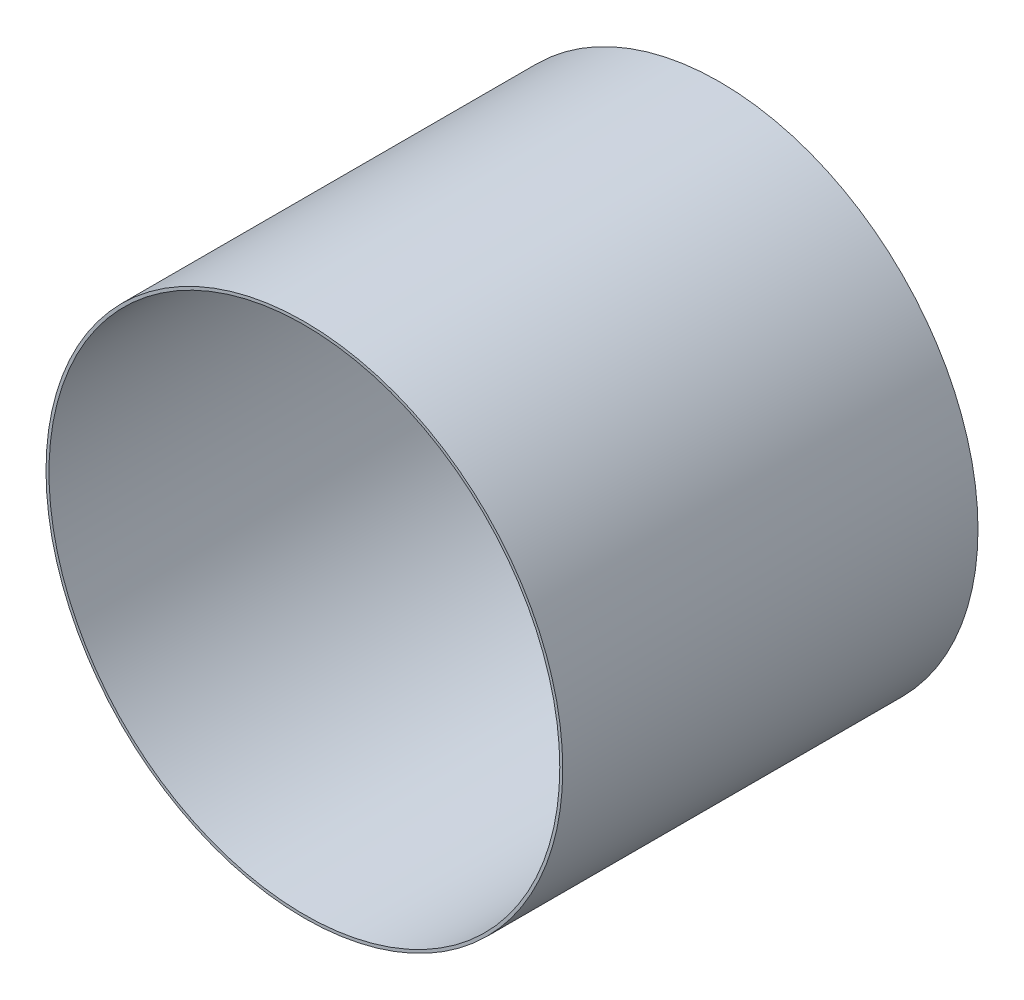
SolidWorks part; units mm, degrees
other "Camera1"
ref_plane "Front Plane" through (0, 0, 0) normal (0, 0, 1) x (1, 0, 0)
ref_plane "Top Plane" through (0, 0, 0) normal (0, 1, 0) x (1, 0, 0)
ref_plane "Right Plane" through (0, 0, 0) normal (1, 0, 0) x (0, 0, -1)
sketch "Sketch1" plane through (0, 0, 0) normal (0, 0, 1) x (1, 0, 0)
  circle A0 centre (0, 0) radius 88.611 construction
  circle A1 centre (0, 0) radius 87.111
  circle A2 centre (0, 0) radius 86.111
  dimension "D1" = 177.222
  dimension "D2" = 1.5
  dimension "D3" = 1
extrude "Boss-Extrude1" add sketch "Sketch1" along normal blind 140
equation "\"OuterThickness\"= 3mm"
equation "\"MasterFillet\"= 3mm"
equation "\"PartSeperation\"= 6mm"
equation "\"Tolerance\"= 0.15mm"
equation "\"HeightPart\"= 100mm"
equation "\"Holes\"= 1.5mm"
equation "\"SpineHolderThickness\"= 3mm"
equation "\"SpineHolderDepth\" = 3mm"
equation "\"MotorLength\" = 40.5mm"
equation "\"MotorWidth\" = 20.3mm"
equation "\"AttachmentHeight\"= 3mm"
equation "\"SpoolDiameter\"= 60mm"
equation "\"SpoolHeight\"= 2mm"
equation "\"SpoolRidgeHeight\"= 1mm"
equation "\"SpoolRidgeDepth\"= 2mm"
equation "\"SpoolSeperation\"= 2mm"
equation "\"ServoHolderWidthOffset\"= 20mm"
equation "\"MotorTransmitterToScrew\"= 21.7mm"
equation "\"SpoolToSpine\"= 15mm"
equation "\"SpoolCenterToMotor\" = 31.5mm"
equation "\"HubOffset\"= 18mm"
equation "\"ServoFastenerHolders\"=2mm"
equation "\"D1@Sketch1\"=2*(((\"SpoolToSpine\"+\"SpoolDiameter\"/2+\"SpoolRidgeDepth\" -\"SpoolCenterToMotor\" -((\"MotorLength\"+\"ServoHolderWidthOffset\")-(\"MotorLength\"+\"Tolerance\"*2))/2 +(\"MotorLength\"+\"ServoHolderWidthOffset\"))^2 + (\"MotorTransmitterToScrew\"+3)^2)^(1/2)+\"HubOffset\")"
equation "\"D1@Boss-Extrude1\"=(3*((\"SpoolDiameter\"/3)*2+\"SpoolRidgeDepth\"*2+\"SpoolSeperation\")+\"SpoolSeperation\")"
equation "\"DiscThickness\"= 4mm"
equation "\"LigamentThickness\"= 2mm"
equation "\"LigamentExtension\"= 1mm"
equation "\"LigamentAngle\"= 20deg"
equation "\"SpineDiameter\"= 15mm"
equation "\"LigamentDepth\"= 1mm"
equation "\"ArduinoLength\" = 53.4mm"
equation "\"ArduinoWidth\" = 50mm"
equation "\"ArdYOffset\" = 29.5mm"
equation "\"ArdXOffset\" = 20.5mm"
equation "\"ArdXOffsetSmall\" = 25mm"
equation "\"MiddleServoOffset\"= 12mm"
equation "\"LargeServoOffset\"= 3mm"
equation "\"SmallServoOffset\"= 0mm"
equation "\"ToolHoleDiameter\"= 12mm"
